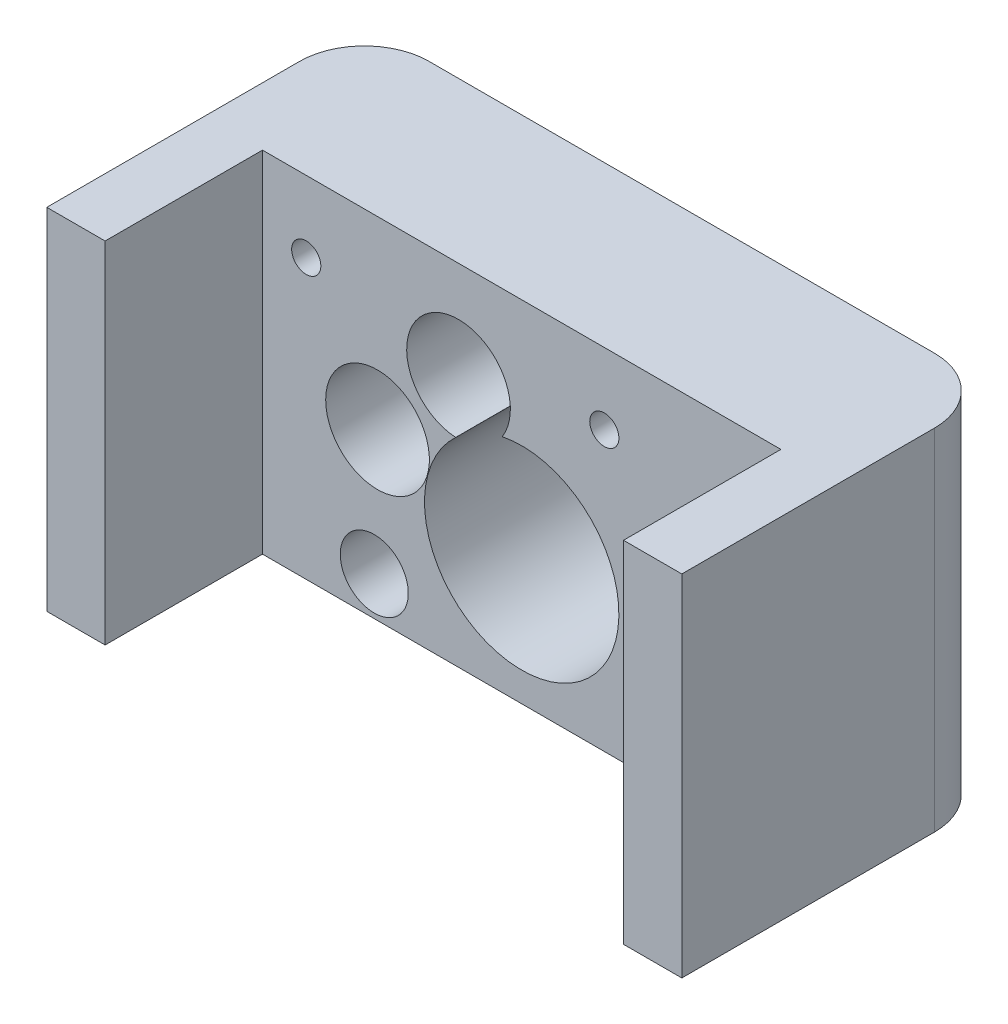
SolidWorks part; units mm, degrees
ref_plane "Front Plane" through (0, 0, 0) normal (0, 0, 1) x (1, 0, 0)
ref_plane "Top Plane" through (0, 0, 0) normal (0, 1, 0) x (1, 0, 0)
ref_plane "Right Plane" through (0, 0, 0) normal (1, 0, 0) x (0, 0, -1)
sketch "Sketch1" plane through (0, 0, 0) normal (0, 0, 1) x (1, 0, 0)
  line L0 (-26.522, 41.4342) -> (-124.522, 41.4342)
  line L1 (-124.522, 41.4342) -> (-124.522, -12.5658)
  line L2 (-124.522, -12.5658) -> (-26.522, -12.5658)
  line L3 (-26.522, -12.5658) -> (-26.522, 41.4342)
  circle A0 centre (-62.772, 30.4342) radius 5.25
  circle A1 centre (-98.272, -6.5658) radius 5.25
  circle A2 centre (-108.772, 30.4342) radius 5.25
  circle A3 centre (-108.772, 30.4342) radius 2.25
  circle A4 centre (-62.772, 30.4342) radius 2.25
  arc A5 (-85.7072, 17.9461) -> (-78.5287, 21.6298) centre (-75.522, 6.9342) ccw
  arc A6 (-78.5287, 21.6298) -> (-85.7072, 17.9461) centre (-85.272, 25.9342) ccw
  circle A7 centre (-97.772, 12.9342) radius 8
  dimension "D1" = 4.5
  dimension "D2" = 10.5
  dimension "D3" = 15
  dimension "D4" = 8
  dimension "D5" = 26.522
  dimension "D6" = 62.772
  dimension "D7" = 75.522
  dimension "D8" = 78.5287
  dimension "D9" = 85.272
  dimension "D10" = 6.9342
  dimension "D11" = 97.772
  dimension "D12" = 98.272
  dimension "D13" = 108.772
  dimension "D14" = 124.522
  dimension "D15" = 12.9342
  dimension "D19" = 30.4342
  dimension "D20" = 41.4342
  dimension "D21" = 6.5658
  dimension "D22" = 12.5658
extrude "Boss-Extrude1" add sketch "Sketch1" along normal blind 49 contours A2 A3 | A0 A4 | L2 L3 L0 L1 A7 A6 A5 A2 A1 A0
fillet "Fillet1" radius 10 2 edges at (-124.522, 14.4342, 0) (-26.522, 14.4342, 0)
sketch "Sketch2" plane through (0, 41.4342, 0) normal (0, 1, 0) x (1, 0, 0)
  line L0 (-26.522, -49) -> (-124.522, -49) construction
  line L1 (-26.522, -49) -> (-26.522, -10) construction
  line L2 (-75.522, -49) -> (-75.522, -27.691) construction
  circle A0 centre (-50.602, -39) radius 1.8109
  circle A1 centre (-100.442, -39) radius 1.8109
  dimension "D1" = 10
  dimension "D2" = 24.08
extrude "Cut-Extrude1" cut sketch "Sketch2" against normal through all
sketch "Sketch3" plane through (0, -12.5658, 0) normal (0, -1, 0) x (1, 0, 0)
  line L0 (-124.522, 49) -> (-26.522, 49) construction
  line L1 (-35.5216, 49) -> (-115.5216, 49)
  line L2 (-35.5216, 49) -> (-35.5216, 24.7099)
  line L3 (-35.5216, 24.7099) -> (-115.5216, 24.7099)
  line L4 (-115.5216, 49) -> (-115.5216, 24.7099)
  line L5 (-35.5216, 44.7099) -> (-35.5216, 24.7099) construction
  point P7 (-35.5256, 49)
extrude "Cut-Extrude2" cut sketch "Sketch3" against normal through all
